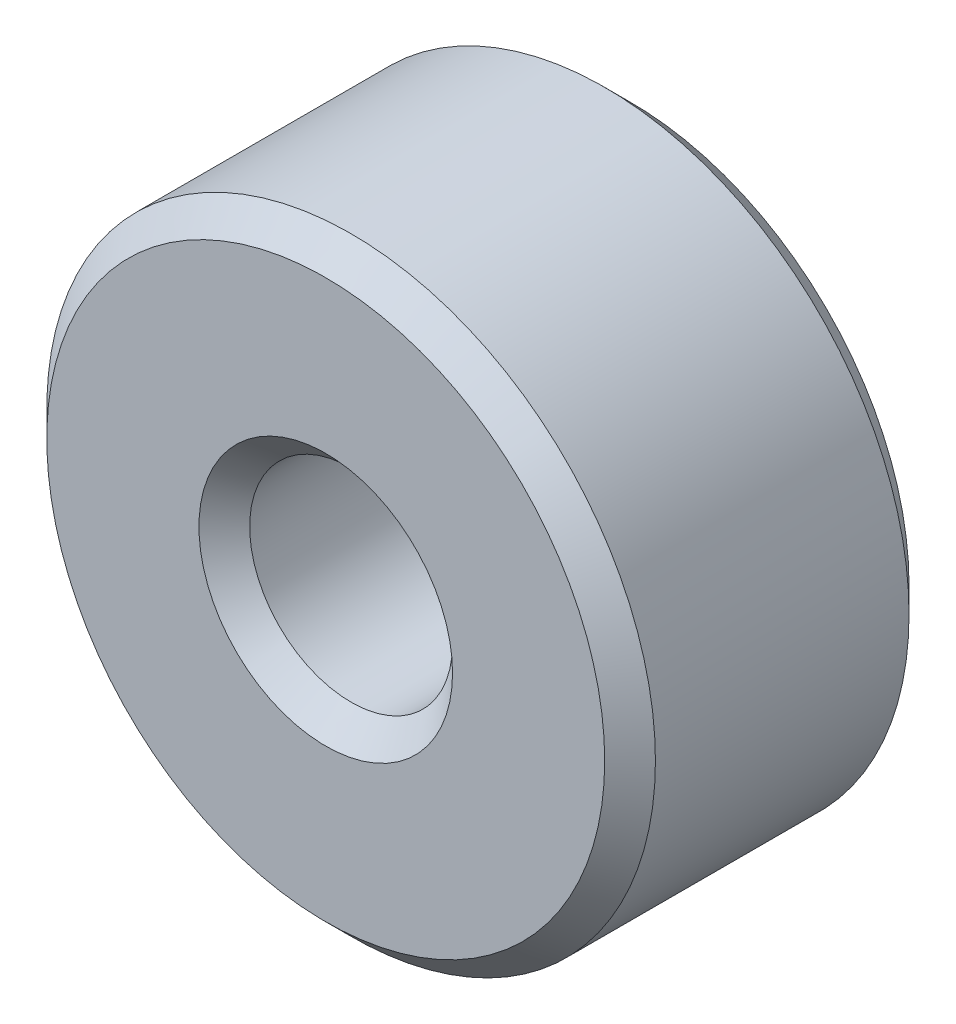
SolidWorks part; units mm, degrees
material "iglide® P210"
ref_plane "Front Plane" through (0, 0, 0) normal (0, 0, 1) x (1, 0, 0)
ref_plane "Top Plane" through (0, 0, 0) normal (0, 1, 0) x (1, 0, 0)
ref_plane "Right Plane" through (0, 0, 0) normal (1, 0, 0) x (0, 0, -1)
sketch "Sketch1" plane through (0, 0, 0) normal (0, 0, 1) x (1, 0, 0)
  circle A0 centre (0, 0) radius 1
  dimension "D1" = 2
extrude "Extrude-Thin1" add sketch "Sketch1" along normal blind 3 thin
chamfer "Chamfer1" distance 0.25 angle 45 4 edges at (1, 0, 0) (3, 0, 0) (1, 0, 3) (3, 0, 3)
